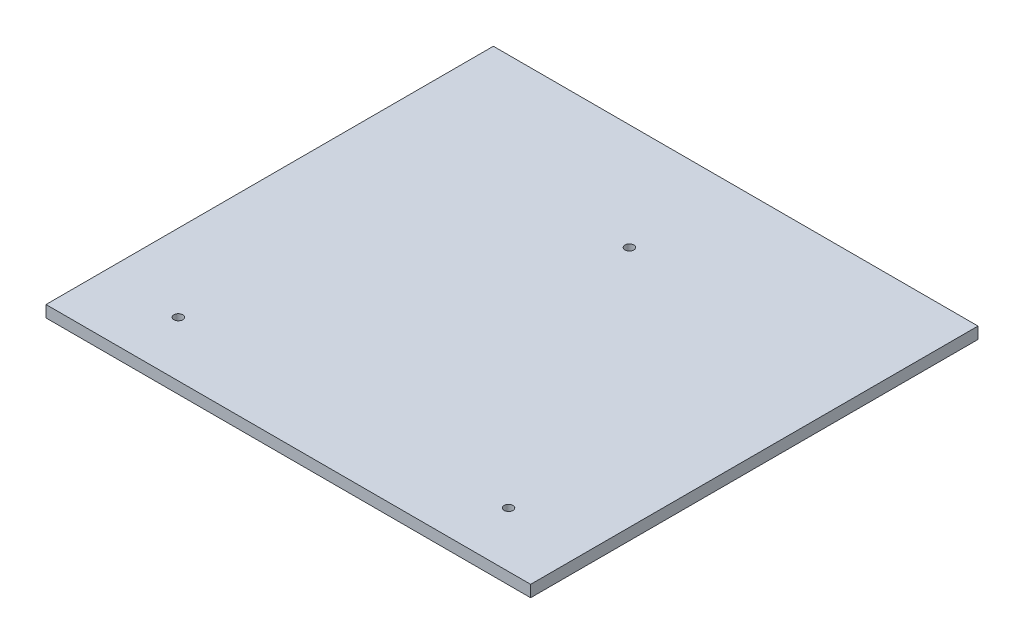
SolidWorks part; units mm, degrees
material "Cedar"
ref_plane "Front Plane" through (0, 0, 0) normal (0, 0, 1) x (1, 0, 0)
ref_plane "Top Plane" through (0, 0, 0) normal (0, 1, 0) x (1, 0, 0)
ref_plane "Right Plane" through (0, 0, 0) normal (1, 0, 0) x (0, 0, -1)
sketch "Sketch1" plane through (0, 0, 0) normal (0, 1, 0) x (1, 0, 0)
  line L1 (0, 0) -> (660.4, 0)
  line L2 (0, 0) -> (0, 609.6)
  line L3 (0, 609.6) -> (660.4, 609.6)
  line L4 (660.4, 0) -> (660.4, 609.6)
  dimension "D1" = 660.4
  dimension "D2" = 609.6
extrude "Boss-Extrude1" add sketch "Sketch1" along normal blind 15.875
sketch "Sketch5" plane through (0, 15.875, 0) normal (0, 1, 0) x (1, 0, 0)
  line L0 (330.2, 609.6) -> (330.2, 464.8281) construction
  line L1 (660.4, 609.6) -> (0, 609.6) construction
  line L2 (0, 0) -> (105.2, 75.1166) construction
  line L3 (660.4, 0) -> (555.2, 75.1166) construction
  line L5 (330.2, 464.8281) -> (105.2, 75.1166) construction
  line L6 (105.2, 75.1166) -> (555.2, 75.1166) construction
  line L7 (555.2, 75.1166) -> (330.2, 464.8281) construction
  line L8 (330.2, 464.8281) -> (330.2, 75.1166) construction
  circle A0 centre (105.2, 75.1166) radius 5.9944
  circle A1 centre (555.2, 75.1166) radius 5.9944
  circle A2 centre (330.2, 464.8281) radius 5.9944
  dimension "D6" = 11.9888
  dimension "D7" = 11.9888
  dimension "D8" = 11.9888
  dimension "D1" = 450
extrude "Cut-Extrude2" cut sketch "Sketch5" against normal through all
sketch "Sketch6" plane through (0, 15.875, 0) normal (0, 1, 0) x (1, 0, 0)
  line L0 (0, 609.6) -> (660.4, 0) construction
  line L1 (660.4, 609.6) -> (0, 0) construction
  point P8 (330.2, 304.8)
sketch "Sketch7" plane through (0, 15.875, 0) normal (0, 1, 0) x (1, 0, 0)
  circle A0 centre (17.9605, 17.9605) radius 17
